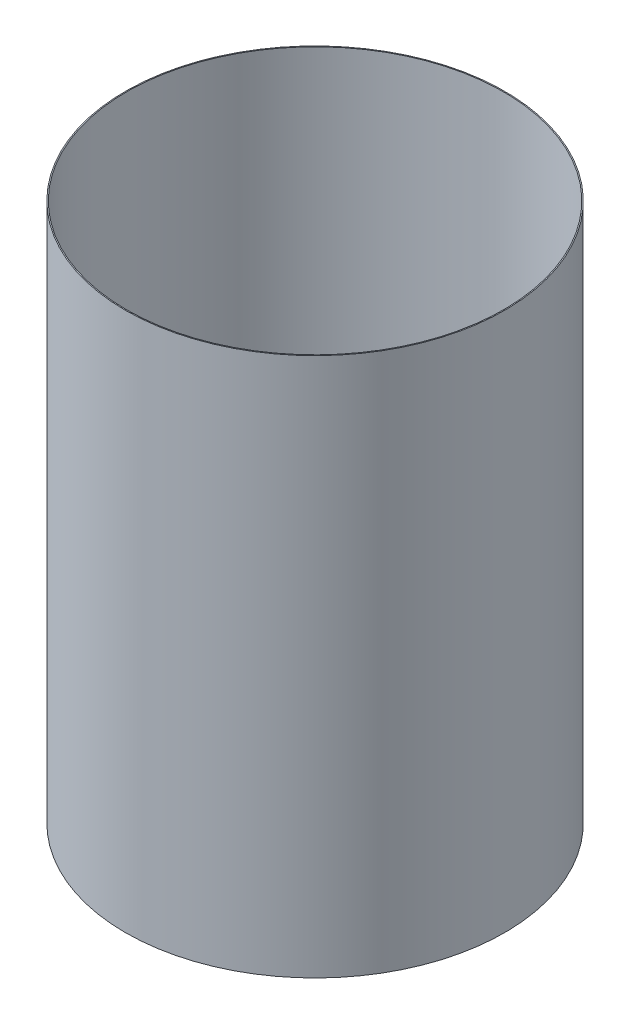
SolidWorks part; units mm, degrees
material "Thornel Mat VMA"
ref_plane "Front Plane" through (0, 0, 0) normal (0, 0, 1) x (1, 0, 0)
ref_plane "Top Plane" through (0, 0, 0) normal (0, 1, 0) x (1, 0, 0)
ref_plane "Right Plane" through (0, 0, 0) normal (1, 0, 0) x (0, 0, -1)
ref_axis "Axis1" through (0, 55, 0) along (0, -1, 0)
sketch "Sketch1" plane through (0, 0, 0) normal (0, 0, 1) x (1, 0, 0)
  line L0 (-46.6725, -19.9059) -> (-46.6725, -153.2559)
  line L2 (-38.1, -19.9059) -> (0, -19.9059) construction
  line L3 (-38.1, -153.2559) -> (0, -153.2559) construction
revolve "Revolve-Thin1" add sketch "Sketch1" angle 360 about axis through (0, 55, 0) along (0, -1, 0)
equation "\"D3@Revolve-Thin1\"=\"CF THICKNESS@Cryo Tank.Assembly\""
